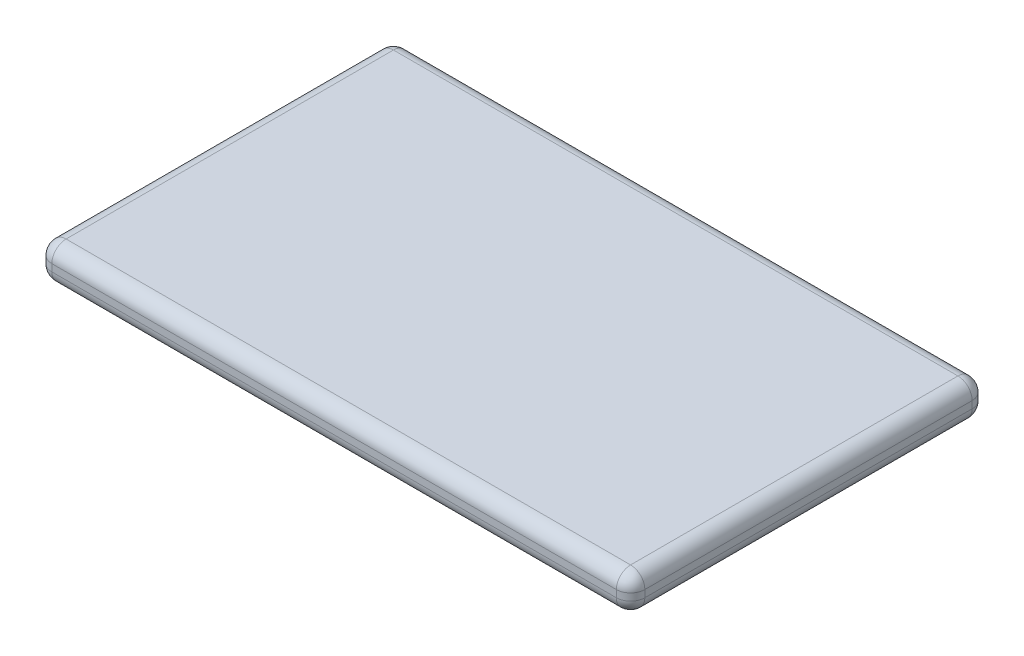
SolidWorks part; units mm, degrees
ref_plane "Front Plane" through (0, 0, 0) normal (0, 0, 1) x (1, 0, 0)
ref_plane "Top Plane" through (0, 0, 0) normal (0, 1, 0) x (1, 0, 0)
ref_plane "Right Plane" through (0, 0, 0) normal (1, 0, 0) x (0, 0, -1)
sketch "Sketch1" plane through (0, 0, 0) normal (0, 1, 0) x (1, 0, 0)
  line L1 (-125, -75) -> (125, -75)
  line L2 (-125, -75) -> (-125, 75)
  line L3 (-125, 75) -> (125, 75)
  line L4 (125, -75) -> (125, 75)
  line L5 (-125, -75) -> (125, 75) construction
  line L6 (-125, 75) -> (125, -75) construction
  point P0 (0, 0)
  dimension "D1" = 250
  dimension "D2" = 150
extrude "Boss-Extrude1" add sketch "Sketch1" along normal blind 15 contours L2 L1 L4 L3
fillet "Fillet1" radius 6 12 edges at (-125, 0, 0) (0, 0, 75) (125, 0, 0) (0, 0, -75) (125, 15, 0) (0, 15, 75) (-125, 15, 0) (0, 15, -75) (-125, 7.5, 75) (125, 7.5, 75) (-125, 7.5, -75) (125, 7.5, -75)
